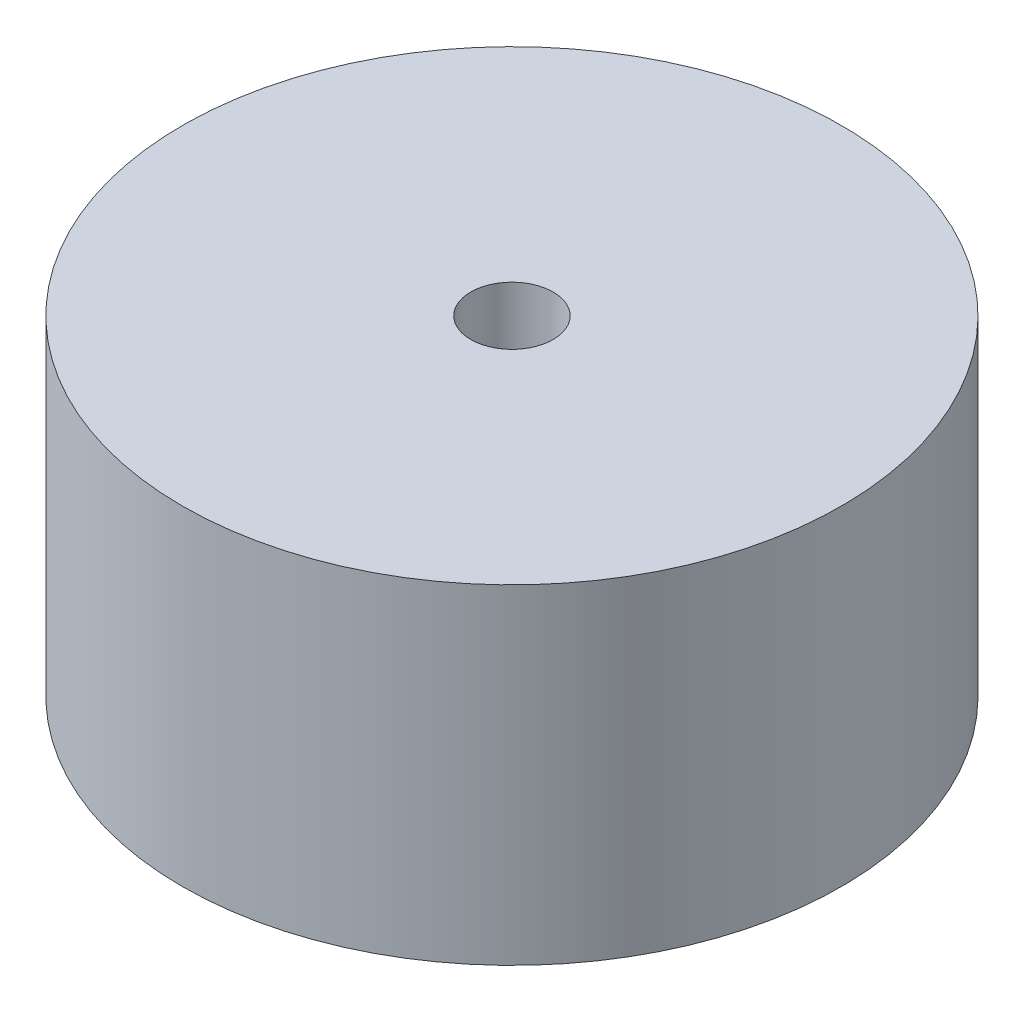
SolidWorks part; units mm, degrees
ref_plane "前视基准面" through (0, 0, 0) normal (0, 0, 1) x (1, 0, 0)
ref_plane "上视基准面" through (0, 0, 0) normal (0, 1, 0) x (1, 0, 0)
ref_plane "右视基准面" through (0, 0, 0) normal (1, 0, 0) x (0, 0, -1)
sketch "草图1" plane through (0, 0, 0) normal (0, 1, 0) x (1, 0, 0)
  circle A0 centre (0, 0) radius 20
  dimension "D1" = 40
extrude "凸台-拉伸1" add sketch "草图1" along normal blind 20
sketch "草图2" plane through (0, 20, 0) normal (0, 1, 0) x (1, 0, 0)
  circle A0 centre (0, 0) radius 2.5
  dimension "D1" = 5
extrude "切除-拉伸1" cut sketch "草图2" against normal blind 10
sketch "草图3" plane through (0, 0, 0) normal (0, -1, 0) x (1, 0, 0)
  circle A0 centre (0, 0) radius 9
  circle A1 centre (0, 0) radius 18
  dimension "D1" = 18
  dimension "D2" = 36
extrude "切除-拉伸2" cut sketch "草图3" against normal blind 2
